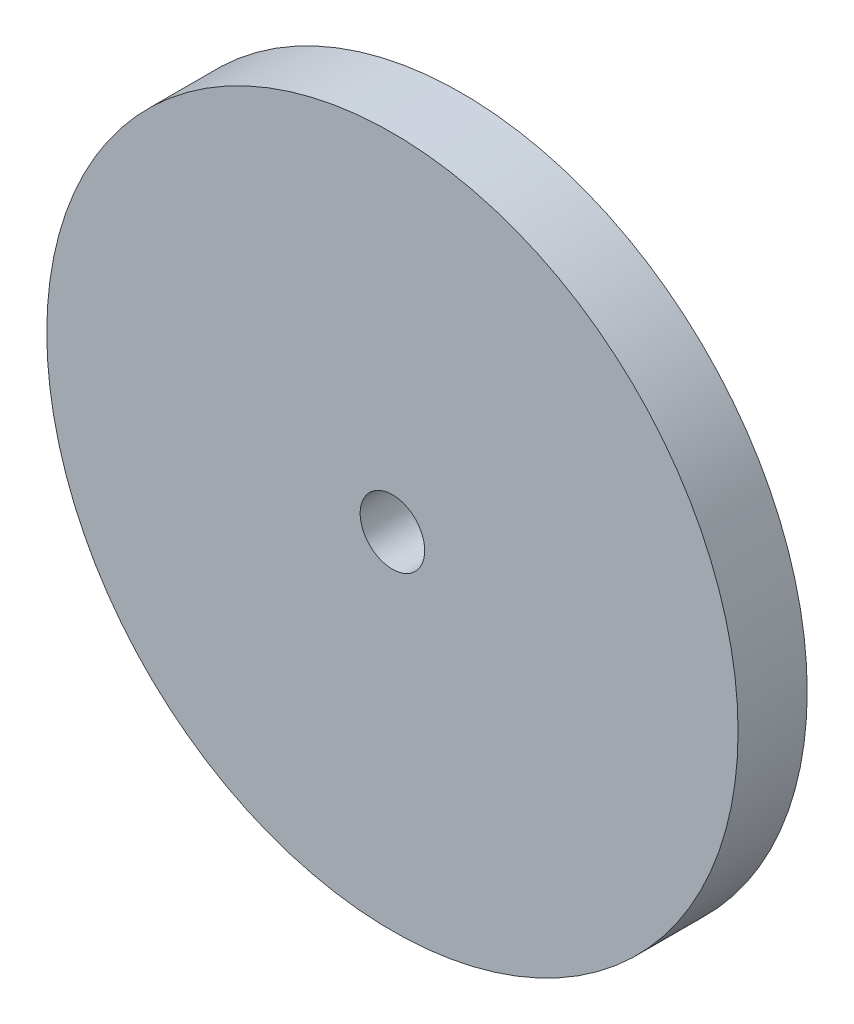
SolidWorks part; units mm, degrees
ref_plane "Plan de face" through (0, 0, 0) normal (0, 0, 1) x (1, 0, 0)
ref_plane "Plan de dessus" through (0, 0, 0) normal (0, 1, 0) x (1, 0, 0)
ref_plane "Plan de droite" through (0, 0, 0) normal (1, 0, 0) x (0, 0, -1)
sketch "Esquisse1" plane through (0, 0, 0) normal (0, 0, 1) x (1, 0, 0)
  circle A0 centre (0, 0) radius 1.4
  circle A1 centre (0, 0) radius 15
  dimension "D1" = 2.8
  dimension "D2" = 30
extrude "Boss.-Extru.1" add sketch "Esquisse1" along normal blind 3
